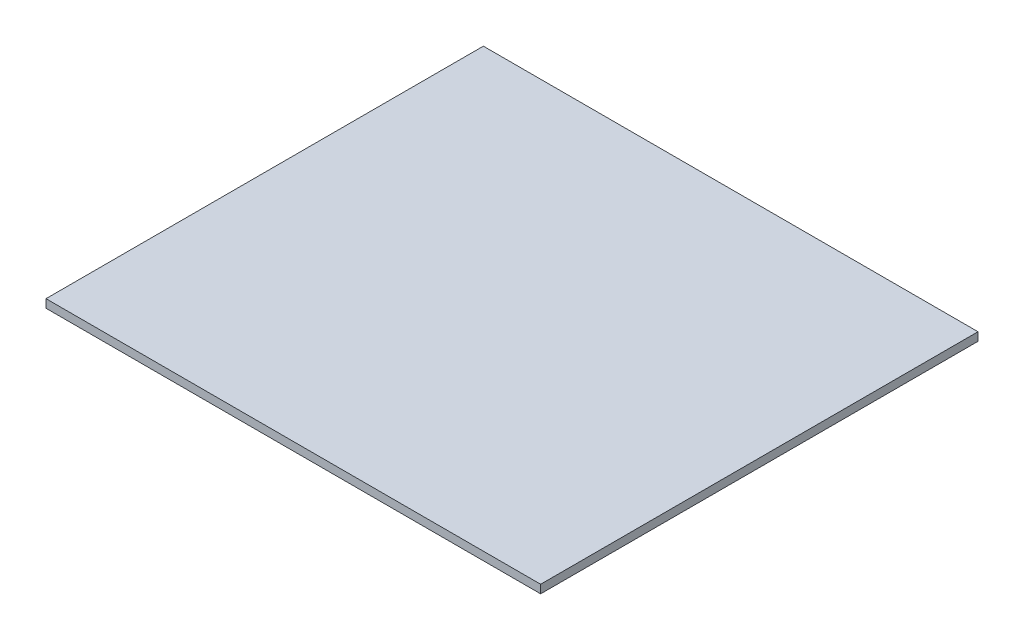
SolidWorks part; units mm, degrees
ref_plane "Front Plane" through (0, 0, 0) normal (0, 0, 1) x (1, 0, 0)
ref_plane "Top Plane" through (0, 0, 0) normal (0, 1, 0) x (1, 0, 0)
ref_plane "Right Plane" through (0, 0, 0) normal (1, 0, 0) x (0, 0, -1)
sketch "Sketch1" plane through (0, 0, 0) normal (0, 1, 0) x (1, 0, 0)
  line L1 (0, 0) -> (950, 0)
  line L2 (0, 0) -> (0, 840)
  line L3 (0, 840) -> (950, 840)
  line L4 (950, 0) -> (950, 840)
  dimension "D1" = 950
  dimension "D2" = 840
extrude "Boss-Extrude1" add sketch "Sketch1" along normal blind 16
